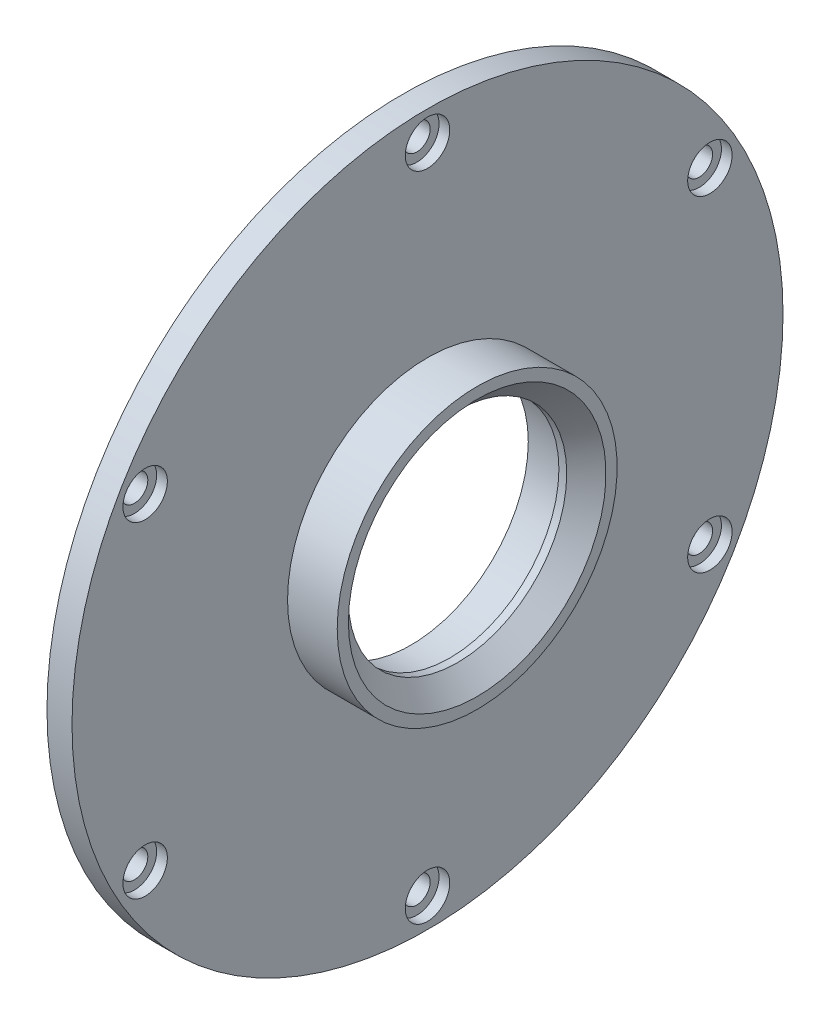
SolidWorks part; units mm, degrees
ref_plane "Front Plane" through (0, 0, 0) normal (0, 0, 1) x (1, 0, 0)
ref_plane "Top Plane" through (0, 0, 0) normal (0, 1, 0) x (1, 0, 0)
ref_plane "Right Plane" through (0, 0, 0) normal (1, 0, 0) x (0, 0, -1)
sketch "Sketch2" plane through (0, 0, 0) normal (0, 0, 1) x (1, 0, 0)
  line L0 (0, 0) -> (58.591, 0) construction
  line L2 (0, 0) -> (18.4, 0)
  line L3 (0, 0) -> (0, 2.5)
  line L4 (0, 2.5) -> (18.4, 2.5)
  line L5 (18.4, 0) -> (18.4, 2.5)
  line L6 (6.0094, 2.5) -> (6.0094, 6)
  line L11 (6.0094, 6) -> (9.9794, 6)
  line L16 (12.9794, 6) -> (12.9794, 3)
  line L17 (12.9794, 3) -> (13.6398, 3)
  line L18 (13.6398, 3) -> (13.6398, 2.5)
  line L19 (13.6398, 2.5) -> (6.0094, 2.5)
  line L22 (13.6398, 2.5) -> (16.1198, 2.5)
  line L23 (13.6398, 2.5) -> (13.6398, 4)
  line L24 (13.6398, 4) -> (16.1198, 4)
  line L25 (16.1198, 2.5) -> (16.1198, 4)
  line L27 (6.0094, 6) -> (9.9794, 6)
  line L28 (6.0094, 6) -> (6.0094, 9)
  line L29 (6.0094, 9) -> (9.9794, 9)
  line L30 (9.9794, 6) -> (9.9794, 9)
  line L31 (6.0094, 9) -> (6.0094, 8.25)
  line L32 (6.0094, 8.25) -> (5.0094, 8.25)
  line L33 (8.6609, 22.001) -> (8.6609, 12.476) construction
  line L34 (5.0094, 12.476) -> (12.3124, 12.476)
  line L35 (9.9794, 9) -> (12.3124, 9)
  line L36 (5.0094, 7.9375) -> (1.7709, 7.9375)
  line L37 (5.0094, 8.25) -> (5.0094, 12.476)
  line L38 (5.0094, 7.9375) -> (5.0094, 13.9365)
  line L39 (5.0094, 13.9365) -> (1.7709, 13.9365)
  line L40 (1.7709, 7.9375) -> (1.7709, 13.9365)
  line L41 (5.0094, 22.001) -> (12.3124, 22.001)
  line L42 (5.0094, 22.001) -> (5.0094, 30.1625)
  line L43 (5.0094, 30.1625) -> (12.3124, 30.1625)
  line L44 (12.3124, 22.001) -> (12.3124, 30.1625)
  line L49 (16.6398, 22.001) -> (16.6398, 7.5)
  line L51 (23.0198, 7.5) -> (23.0198, 6.5)
  line L54 (16.1198, 4) -> (13.6398, 4)
  line L56 (18.0398, 7.5) -> (23.0198, 7.5)
  line L57 (13.3124, 22.001) -> (16.6398, 22.001)
  line L58 (16.1198, 3.5) -> (20.0198, 3.5)
  line L59 (29.9098, 14) -> (26.9098, 11)
  line L60 (4.0094, 31.75) -> (18.0398, 31.75)
  line L61 (18.0398, 7.5) -> (23.0198, 7.5)
  line L62 (18.0398, 7.5) -> (18.0398, 12)
  line L63 (18.0398, 12) -> (23.0198, 12)
  line L64 (23.0198, 7.5) -> (23.0198, 12)
  line L65 (18.0398, 31.75) -> (18.0398, 12)
  line L66 (23.0198, 11) -> (26.9098, 11)
  line L67 (34.8098, 23) -> (31.3098, 19.5)
  line L68 (35.8098, 31) -> (38.7998, 33.99)
  line L69 (29.9098, 14) -> (29.9098, 15)
  line L70 (29.9098, 15) -> (22.9398, 15)
  line L71 (22.9398, 15) -> (21.0398, 15)
  line L72 (18.0398, 7.5) -> (16.6398, 7.5)
  line L73 (21.0398, 15) -> (21.0398, 43)
  line L74 (19.6115, 40) -> (9.6516, 40)
  line L75 (9.6516, 40) -> (4.0094, 40)
  line L76 (21.0398, 43) -> (19.6115, 43)
  line L77 (22.9398, 15) -> (29.9098, 15)
  line L78 (22.9398, 15) -> (22.9398, 21)
  line L79 (22.9398, 21) -> (29.9098, 21)
  line L80 (29.9098, 15) -> (29.9098, 21)
  line L81 (9.6516, 40) -> (19.6115, 40)
  line L82 (9.6516, 40) -> (9.6516, 50)
  line L83 (9.6516, 50) -> (19.6115, 50)
  line L84 (19.6115, 40) -> (19.6115, 50)
  line L85 (4.0094, 40) -> (4.0094, 31.75)
  line L86 (12.9794, 3) -> (12.9794, 2.5)
  line L87 (31.3098, 19.5) -> (29.9098, 19.5)
  line L88 (21.4694, 63.5) -> (21.4694, 51.308)
  line L89 (21.4694, 63.5) -> (25.9398, 63.5)
  line L90 (25.9398, 63.5) -> (25.9398, 25)
  line L91 (27.8398, 25) -> (25.9398, 25)
  line L92 (9.6516, 48) -> (8.2233, 48)
  line L93 (8.2233, 48) -> (8.2233, 53.476)
  line L94 (8.2233, 53.476) -> (19.6115, 53.476)
  line L95 (19.6115, 53.476) -> (19.6115, 50)
  line L96 (13.9174, 63.001) -> (13.9174, 53.476) construction
  line L97 (8.2233, 63.001) -> (19.6115, 63.001)
  line L98 (8.2233, 63.001) -> (8.2233, 68.2625)
  line L99 (8.2233, 68.2625) -> (19.6115, 68.2625)
  line L100 (19.6115, 63.001) -> (19.6115, 68.2625)
  line L101 (12.9794, 6) -> (11.9794, 6)
  line L102 (8.2233, 44.825) -> (4.9848, 44.825)
  line L103 (8.2233, 44.825) -> (8.2233, 54.9365)
  line L104 (8.2233, 54.9365) -> (4.9848, 54.9365)
  line L106 (9.9794, 6) -> (10.8794, 6)
  line L107 (27.8398, 25) -> (34.8098, 25)
  line L108 (34.8098, 25) -> (34.8098, 23)
  line L109 (0, 0) -> (-2, 0)
  line L110 (0, 0) -> (0, 11)
  line L111 (27.8398, 25) -> (34.8098, 25)
  line L112 (27.8398, 25) -> (27.8398, 32.5)
  line L113 (27.8398, 32.5) -> (34.8098, 32.5)
  line L114 (34.8098, 25) -> (34.8098, 32.5)
  line L115 (35.8098, 31) -> (34.8098, 31)
  line L116 (27.8398, 32.5) -> (27.8398, 64.5)
  line L117 (20.5849, 74.025) -> (6.2499, 74.025)
  line L118 (6.2499, 74.025) -> (6.2499, 76.2)
  line L119 (38.7998, 47.29) -> (30.8398, 55.25)
  line L120 (0, 11) -> (-2, 11)
  line L121 (38.7998, 43.815) -> (30.8623, 43.815)
  line L123 (-4.8152, 69.85) -> (1.5348, 76.2)
  line L124 (38.7998, 47.29) -> (38.7998, 33.99)
  line L125 (-2, 0) -> (-2, 11)
  line L126 (38.7998, 37.465) -> (30.8623, 37.465)
  line L127 (30.8623, 43.815) -> (30.8623, 37.465)
  line L128 (6.0094, 2.5) -> (6.0094, 0)
  line L129 (-0.0152, 63.5) -> (-0.0152, 30)
  line L132 (4.9848, 63.5) -> (-0.0152, 63.5)
  line L136 (-1.8152, 30) -> (-11.7752, 30)
  line L138 (-13.7752, 25.4) -> (-2, 25.4)
  line L139 (-2, 25.4) -> (-2, 11.5)
  line L140 (27.8398, 64.5) -> (20.5849, 64.5)
  line L141 (-1.8152, 30) -> (-11.7752, 30)
  line L142 (-1.8152, 30) -> (-1.8152, 39)
  line L143 (-1.8152, 39) -> (-11.7752, 39)
  line L144 (-11.7752, 30) -> (-11.7752, 39)
  line L145 (20.5849, 64.5) -> (20.5849, 74.025)
  line L146 (-12.7752, 37) -> (-12.7752, 47.29)
  line L147 (-12.7752, 37) -> (-11.7752, 37)
  line L148 (30.8398, 55.25) -> (30.8398, 76.2)
  line L149 (11.9794, 6) -> (11.9794, 5.45)
  line L154 (-2, 11.5) -> (0.5, 11.5)
  line L155 (4.9848, 60.6197) -> (24.0348, 60.6197)
  line L160 (4.9848, 60.6197) -> (4.9848, 55.8572)
  line L161 (4.9848, 55.8572) -> (24.0348, 55.8572)
  line L166 (24.0348, 60.6197) -> (24.0348, 55.8572)
  line L167 (4.9848, 60.6197) -> (24.0348, 55.8572) construction
  line L172 (4.9848, 55.8572) -> (24.0348, 60.6197) construction
  line L173 (24.0348, 62.2072) -> (25.9398, 62.2072)
  line L174 (11.9794, 5.45) -> (10.8794, 5.45)
  line L175 (10.8794, 6) -> (10.8794, 5.45)
  line L176 (24.0348, 62.2072) -> (24.0348, 54.2697)
  line L177 (24.0348, 54.2697) -> (25.9398, 54.2697)
  line L178 (25.9398, 62.2072) -> (25.9398, 54.2697)
  line L179 (24.0348, 62.2072) -> (25.9398, 54.2697) construction
  line L180 (24.0348, 54.2697) -> (25.9398, 62.2072) construction
  line L181 (3, 19.6197) -> (15.7, 19.6197)
  line L182 (3, 19.6197) -> (3, 14.8572)
  line L183 (3, 14.8572) -> (15.7, 14.8572)
  line L184 (15.7, 19.6197) -> (15.7, 14.8572)
  line L185 (3, 19.6197) -> (15.7, 14.8572) construction
  line L186 (3, 14.8572) -> (15.7, 19.6197) construction
  line L187 (15.7, 21.2072) -> (16.6398, 21.2072)
  line L188 (15.7, 21.2072) -> (15.7, 13.2697)
  line L189 (15.7, 13.2697) -> (16.6398, 13.2697)
  line L190 (16.6398, 21.2072) -> (16.6398, 13.2697)
  line L191 (15.7, 21.2072) -> (16.6398, 13.2697) construction
  line L192 (15.7, 13.2697) -> (16.6398, 21.2072) construction
  line L193 (0.5, 11.5) -> (0.5, 6.9375)
  line L194 (0.5, 6.9375) -> (1.7709, 6.9375)
  line L195 (23.0198, 6.5) -> (20.0198, 3.5)
  line L196 (4.9848, 63.5) -> (4.9848, 54.9365)
  line L197 (3, 43.825) -> (4.9848, 43.825)
  line L198 (1.7709, 6.9375) -> (1.7709, 7.9375)
  line L199 (6.0094, 0) -> (12.9794, 0)
  line L200 (12.9794, 0) -> (12.9794, 2.5)
  line L201 (18.0398, 31.75) -> (18.0398, 35.875)
  line L202 (18.0398, 35.875) -> (21.0398, 35.875)
  line L203 (30.8398, 76.2) -> (6.2499, 76.2)
  line L204 (2.8049, 69.85) -> (7.2499, 69.85) construction
  line L205 (7.2499, 67.4688) -> (26.2999, 67.4688)
  line L206 (7.2499, 74.025) -> (7.2499, 64.5)
  line L207 (7.2499, 64.5) -> (-1.8152, 64.5)
  line L208 (-1.8152, 64.5) -> (-1.8152, 39)
  line L209 (-12.7752, 47.29) -> (-4.8152, 55.25)
  line L210 (-4.8152, 55.25) -> (-4.8152, 69.85)
  line L211 (7.2499, 67.4688) -> (7.2499, 72.2312)
  line L212 (7.2499, 72.2312) -> (26.2999, 72.2313)
  line L213 (26.2999, 67.4688) -> (26.2999, 72.2313)
  line L214 (26.2999, 73.8187) -> (30.8398, 73.8187)
  line L215 (26.2999, 73.8187) -> (26.2999, 65.8813)
  line L216 (26.2999, 65.8813) -> (30.8398, 65.8813)
  line L217 (30.8398, 73.8187) -> (30.8398, 65.8813)
  line L218 (2.8049, 72.2313) -> (25.0299, 72.2313)
  line L219 (2.8049, 72.2313) -> (2.8049, 67.4687)
  line L220 (2.8049, 67.4687) -> (25.0299, 67.4687)
  line L221 (25.0299, 72.2313) -> (25.0299, 67.4687)
  line L222 (25.0299, 69.85) -> (20.5849, 69.85) construction
  line L223 (21.4694, 51.308) -> (22.9398, 51.308)
  line L224 (22.9398, 51.308) -> (22.9398, 21)
  line L225 (13.6398, 4) -> (13.6398, 12.2697)
  line L226 (13.6398, 12.2697) -> (13.3124, 12.2697)
  line L227 (13.3124, 12.2697) -> (13.3124, 22.001)
  line L228 (12.3124, 9) -> (12.3124, 12.476)
  line L229 (-1.8152, 30) -> (-0.0152, 30)
  line L230 (8.2233, 65.6317) -> (2.8049, 65.6317) construction
  line L231 (19.6115, 65.6317) -> (25.0299, 65.6317) construction
  line L232 (1.5348, 76.2) -> (6.2499, 76.2)
  line L233 (-11.7752, 30) -> (-13.7752, 30)
  line L234 (-13.7752, 30) -> (-13.7752, 25.4)
  line L235 (3, 13.9365) -> (3, 43.825)
  line L236 (4.9848, 54.9365) -> (4.9848, 44.825)
  line L237 (4.9848, 43.825) -> (4.9848, 44.825)
  circle A0 centre (26.8898, 25.95) radius 0.95
  circle A1 centre (21.9898, 15.95) radius 0.95
  circle A2 centre (17.3398, 8.2) radius 0.7
  circle A3 centre (10.4294, 6.45) radius 0.45
  circle A4 centre (-0.9152, 30.9) radius 0.9
  point P7 (24.9873, 58.2385)
  point P131 (16.1699, 17.2385)
  point P135 (14.5098, 58.2385)
  point P146 (9.35, 17.2385)
sketch "Sketch3" plane through (0, 0, 0) normal (0, 0, 1) x (1, 0, 0)
  line L0 (34.8098, 25) -> (34.8098, 23) construction
  line L4 (29.9098, 15) -> (29.9098, 21) construction
  line L5 (31.3098, 19.5) -> (29.9098, 19.5) construction
  line L6 (34.8098, 23) -> (31.3098, 19.5) construction
  line L7 (22.9398, 21) -> (29.9098, 21) construction
  line L11 (34.8098, 25) -> (34.8098, 23)
  line L15 (29.9098, 19.5) -> (29.9098, 21)
  line L16 (31.3098, 19.5) -> (29.9098, 19.5)
  line L17 (34.8098, 23) -> (31.3098, 19.5)
  line L18 (22.9398, 21) -> (29.9098, 21)
  line L22 (27.8398, 25) -> (25.9398, 25) construction
  line L23 (27.8398, 25) -> (34.8098, 25) construction
  line L24 (25.9398, 63.5) -> (25.9398, 25) construction
  line L25 (22.9398, 51.308) -> (22.9398, 21) construction
  line L26 (21.4694, 51.308) -> (22.9398, 51.308) construction
  line L27 (21.4694, 63.5) -> (21.4694, 51.308) construction
  line L28 (21.4694, 63.5) -> (25.9398, 63.5) construction
  line L29 (27.8398, 25) -> (25.9398, 25)
  line L30 (27.8398, 25) -> (34.8098, 25)
  line L31 (25.9398, 63.5) -> (25.9398, 25)
  line L32 (22.9398, 51.308) -> (22.9398, 21)
  line L33 (21.4694, 51.308) -> (22.9398, 51.308)
  line L34 (21.4694, 63.5) -> (21.4694, 51.308)
  line L35 (21.4694, 63.5) -> (25.9398, 63.5)
revolve "Revolve1" add sketch "Sketch3" angle 360 about L0
sketch "Sketch4" plane through (0, 0, 0) normal (1, 0, 0) x (0, 0, -1)
  line L0 (0, 0) -> (0, 69.85) construction
  line L1 (0, 0) -> (13.6271, 68.5079) construction
  line L2 (0, 0) -> (0, 58.2385) construction
  line L3 (0, 0) -> (50.436, 29.1192) construction
  line L4 (0, 0) -> (0, 31.75) construction
  line L5 (0, 0) -> (12.1502, 29.3332) construction
  line L6 (0, 0) -> (0, 17.2385) construction
  line L7 (0, 0) -> (14.929, 8.6192) construction
  line L8 (0, 0) -> (0, 58.2385) construction
  line L9 (0, 0) -> (50.436, 29.1192) construction
  line L10 (0, 0) -> (5.9583, 29.9542) construction
  line L11 (0, 0) -> (16.9677, 25.394) construction
  circle A0 centre (0, 0) radius 69.85 construction
  circle A1 centre (0, 0) radius 58.2385 construction
  circle A2 centre (0, 0) radius 31.75 construction
  circle A3 centre (0, 0) radius 17.2385 construction
  circle A4 centre (0, 69.85) radius 3.175
  circle A5 centre (0, 58.2385) radius 4.7625
  circle A6 centre (0, 31.75) radius 3.175
  circle A7 centre (0, 17.2385) radius 4.7625
  circle A8 centre (13.6271, 68.5079) radius 3.175
  circle A9 centre (26.7304, 64.533) radius 3.175
  circle A10 centre (38.8066, 58.0782) radius 3.175
  circle A11 centre (49.3914, 49.3914) radius 3.175
  circle A12 centre (58.0782, 38.8066) radius 3.175
  circle A13 centre (64.533, 26.7304) radius 3.175
  circle A14 centre (68.5079, 13.6271) radius 3.175
  circle A15 centre (69.85, 0) radius 3.175
  circle A16 centre (68.5079, -13.6271) radius 3.175
  circle A17 centre (64.533, -26.7304) radius 3.175
  circle A18 centre (58.0782, -38.8066) radius 3.175
  circle A19 centre (49.3914, -49.3914) radius 3.175
  circle A20 centre (38.8066, -58.0782) radius 3.175
  circle A21 centre (26.7304, -64.533) radius 3.175
  circle A22 centre (13.6271, -68.5079) radius 3.175
  circle A23 centre (0, -69.85) radius 3.175
  circle A24 centre (-13.6271, -68.5079) radius 3.175
  circle A25 centre (-26.7304, -64.533) radius 3.175
  circle A26 centre (-38.8066, -58.0782) radius 3.175
  circle A27 centre (-49.3914, -49.3914) radius 3.175
  circle A28 centre (-58.0782, -38.8066) radius 3.175
  circle A29 centre (-64.533, -26.7304) radius 3.175
  circle A30 centre (-68.5079, -13.6271) radius 3.175
  circle A31 centre (-69.85, 0) radius 3.175
  circle A32 centre (-68.5079, 13.6271) radius 3.175
  circle A33 centre (-64.533, 26.7304) radius 3.175
  circle A34 centre (-58.0782, 38.8066) radius 3.175
  circle A35 centre (-49.3914, 49.3914) radius 3.175
  circle A36 centre (-38.8066, 58.0782) radius 3.175
  circle A37 centre (-26.7304, 64.533) radius 3.175
  circle A38 centre (-13.6271, 68.5079) radius 3.175
  circle A47 centre (50.436, 29.1192) radius 4.7625
  circle A48 centre (50.436, -29.1192) radius 4.7625
  circle A49 centre (0, -58.2385) radius 4.7625
  circle A50 centre (-50.436, -29.1192) radius 4.7625
  circle A51 centre (-50.436, 29.1192) radius 4.7625
  circle A58 centre (12.1502, 29.3332) radius 3.175
  circle A59 centre (22.4506, 22.4506) radius 3.175
  circle A60 centre (29.3332, 12.1502) radius 3.175
  circle A61 centre (31.75, 0) radius 3.175
  circle A62 centre (29.3332, -12.1502) radius 3.175
  circle A63 centre (22.4506, -22.4506) radius 3.175
  circle A64 centre (12.1502, -29.3332) radius 3.175
  circle A65 centre (0, -31.75) radius 3.175
  circle A66 centre (-12.1502, -29.3332) radius 3.175
  circle A67 centre (-22.4506, -22.4506) radius 3.175
  circle A68 centre (-29.3332, -12.1502) radius 3.175
  circle A69 centre (-31.75, 0) radius 3.175
  circle A70 centre (-29.3332, 12.1502) radius 3.175
  circle A71 centre (-22.4506, 22.4506) radius 3.175
  circle A72 centre (14.929, 8.6192) radius 4.7625
  circle A73 centre (14.929, -8.6192) radius 4.7625
  circle A74 centre (0, -17.2385) radius 4.7625
  circle A75 centre (-14.929, -8.6192) radius 4.7625
  circle A76 centre (-14.929, 8.6192) radius 4.7625
  circle A77 centre (0, 0) radius 50
  circle A78 centre (0, 0) radius 9
  circle A79 centre (-12.1502, 29.3332) radius 3.175
  circle A80 centre (0, 0) radius 76.2
  circle A81 centre (0, 0) radius 74.025
  circle A82 centre (0, 69.85) radius 3.9687
  circle A83 centre (49.3914, 49.3914) radius 3.9687
  circle A84 centre (69.85, 0) radius 3.9688
  circle A85 centre (49.3914, -49.3914) radius 3.9687
  circle A86 centre (0, -69.85) radius 3.9687
  circle A87 centre (-49.3914, -49.3914) radius 3.9687
  circle A88 centre (-69.85, 0) radius 3.9688
  circle A89 centre (-49.3914, 49.3914) radius 3.9687
  circle A90 centre (0, 69.85) radius 2.3812
  circle A91 centre (13.6271, 68.5079) radius 2.3812
  circle A92 centre (26.7304, 64.533) radius 2.3813
  circle A93 centre (38.8066, 58.0782) radius 2.3812
  circle A94 centre (49.3914, 49.3914) radius 2.3812
  circle A95 centre (58.0782, 38.8066) radius 2.3812
  circle A96 centre (64.533, 26.7304) radius 2.3813
  circle A97 centre (68.5079, 13.6271) radius 2.3813
  circle A98 centre (69.85, 0) radius 2.3813
  circle A99 centre (68.5079, -13.6271) radius 2.3813
  circle A100 centre (64.533, -26.7304) radius 2.3813
  circle A101 centre (58.0782, -38.8066) radius 2.3812
  circle A102 centre (49.3914, -49.3914) radius 2.3812
  circle A103 centre (38.8066, -58.0782) radius 2.3812
  circle A104 centre (26.7304, -64.533) radius 2.3813
  circle A105 centre (13.6271, -68.5079) radius 2.3812
  circle A106 centre (0, -69.85) radius 2.3812
  circle A107 centre (-13.6271, -68.5079) radius 2.3812
  circle A108 centre (-26.7304, -64.533) radius 2.3813
  circle A109 centre (-38.8066, -58.0782) radius 2.3812
  circle A110 centre (-49.3914, -49.3914) radius 2.3812
  circle A111 centre (-58.0782, -38.8066) radius 2.3812
  circle A112 centre (-64.533, -26.7304) radius 2.3812
  arc A113 (3.0399, 30.8338) -> (8.9911, 29.65) centre (5.9583, 29.9542) cw
  arc A114 (14.6081, 27.3234) -> (19.6532, 23.9523) centre (16.9677, 25.394) cw
  arc A115 (23.9523, 19.6532) -> (27.3234, 14.6081) centre (25.394, 16.9677) cw
  arc A116 (29.65, 8.9911) -> (30.8338, 3.0399) centre (29.9542, 5.9583) cw
  arc A117 (30.8338, -3.0399) -> (29.65, -8.9911) centre (29.9542, -5.9583) cw
  arc A118 (27.3234, -14.6081) -> (23.9523, -19.6532) centre (25.394, -16.9677) cw
  arc A119 (19.6532, -23.9523) -> (14.6081, -27.3234) centre (16.9677, -25.394) cw
  arc A120 (8.9911, -29.65) -> (3.0399, -30.8338) centre (5.9583, -29.9542) cw
  arc A121 (-3.0399, -30.8338) -> (-8.9911, -29.65) centre (-5.9583, -29.9542) cw
  arc A122 (-14.6081, -27.3234) -> (-19.6532, -23.9523) centre (-16.9677, -25.394) cw
  arc A123 (-23.9523, -19.6532) -> (-27.3234, -14.6081) centre (-25.394, -16.9677) cw
  arc A124 (-29.65, -8.9911) -> (-30.8338, -3.0399) centre (-29.9542, -5.9583) cw
  arc A125 (-30.8338, 3.0399) -> (-29.65, 8.9911) centre (-29.9542, 5.9583) cw
  arc A126 (-27.3234, 14.6081) -> (-23.9523, 19.6532) centre (-25.394, 16.9677) cw
  arc A127 (-19.6532, 23.9523) -> (-14.6081, 27.3234) centre (-16.9677, 25.394) cw
  arc A128 (-8.9911, 29.65) -> (-3.0399, 30.8338) centre (-5.9583, 29.9542) cw
  arc A129 (26.9875, 0) -> (26.9932, 0.1932) centre (30.2705, 0) cw
  arc A130 (65.0988, 0.2771) -> (65.0875, 0) centre (68.4964, 0) ccw
  circle A131 centre (1.5875, 0) radius 40
  circle A132 centre (1.5875, 0) radius 2.5
  circle A133 centre (1.5875, 0) radius 3
  circle A134 centre (1.5875, 0) radius 43
  circle A135 centre (-68.5079, -13.6271) radius 2.3813
  circle A136 centre (-69.85, 0) radius 2.3813
  circle A137 centre (-68.5079, 13.6271) radius 2.3813
  circle A138 centre (-64.533, 26.7304) radius 2.3812
  circle A139 centre (-58.0782, 38.8066) radius 2.3812
  circle A140 centre (-49.3914, 49.3914) radius 2.3812
  circle A141 centre (-38.8066, 58.0782) radius 2.3812
  circle A142 centre (-26.7304, 64.533) radius 2.3813
  circle A143 centre (-13.6271, 68.5079) radius 2.3812
  circle A144 centre (0, 58.2385) radius 2.3812
  circle A145 centre (0, 58.2385) radius 3.9688
  circle A146 centre (50.436, 29.1192) radius 3.9688
  circle A147 centre (50.436, 29.1192) radius 2.3813
  circle A148 centre (50.436, -29.1192) radius 3.9687
  circle A149 centre (50.436, -29.1192) radius 2.3812
  circle A150 centre (0, -58.2385) radius 3.9687
  circle A151 centre (0, -58.2385) radius 2.3812
  circle A152 centre (-50.436, -29.1192) radius 3.9687
  circle A153 centre (-50.436, -29.1192) radius 2.3812
  circle A154 centre (-50.436, 29.1192) radius 3.9687
  circle A155 centre (-50.436, 29.1192) radius 2.3812
  spline S1 degree 4 poles (26.9875, 0) (26.9875, -0.0248) (26.9882, -0.0743) (26.9912, -0.1613) (26.9992, -0.2849) (27.0142, -0.4323) (27.0403, -0.5994) (27.0821, -0.7965) (27.1455, -1.0177) (27.2241, -1.2336) (27.3173, -1.4437) (27.4329, -1.6623) (27.5739, -1.8864) (27.7427, -2.1125) (27.9417, -2.3365) (28.1305, -2.5184) (28.3007, -2.6647) (28.4457, -2.7828) (28.5617, -2.8775) (28.6745, -2.9758) (28.7813, -3.0807) (28.9057, -3.2206) (29.0482, -3.4108) (29.197, -3.6576) (29.3758, -4.0447) (29.5291, -4.5502) (29.6152, -5.1612) (29.5933, -5.8758) (29.4507, -6.5869) (29.186, -7.2733) (28.8461, -7.831) (28.4818, -8.2549) (28.1375, -8.5536) (27.8792, -8.7284) (27.6484, -8.8496) (27.4154, -8.9438) (27.2144, -9.0029) (27.0118, -9.0554) (26.7709, -9.1263) (26.5334, -9.2082) (26.2634, -9.3231) (25.9685, -9.4827) (25.5538, -9.7623) (25.0678, -10.2216) (24.6281, -10.8948) (24.3613, -11.7878) (24.3459, -12.6097) (24.4764, -13.2366) (24.6525, -13.7006) (24.8058, -14.0202) (24.9382, -14.271) (25.0503, -14.5321) (25.1258, -14.8064) (25.1736, -15.0995) (25.1911, -15.4094) (25.1742, -15.8163) (25.0891, -16.3148) (24.907, -16.8764) (24.5182, -17.6315) (23.9757, -18.2942) (23.3695, -18.7764) (22.7564, -19.084) (22.3641, -19.2199) (22.0554, -19.2923) (21.7533, -19.3289) (21.4612, -19.3296) (21.1723, -19.2896) (20.8852, -19.2417) (20.5956, -19.2104) (20.3043, -19.1994) (19.8669, -19.2177) (19.2899, -19.3231) (18.5833, -19.6092) (17.8444, -20.1834) (17.3807, -20.828) (17.1316, -21.424) (17.0182, -21.8879) (16.9714, -22.1971) (16.9537, -22.4701) (16.9533, -22.7044) (16.9619, -22.9384) (16.9737, -23.1333) (16.977, -23.3286) (16.9594, -23.5624) (16.9177, -23.8101) (16.834, -24.1055) (16.6578, -24.5276) (16.3623, -25.0151) (15.9278, -25.5198) (15.3432, -25.99) (14.6957, -26.3472) (14.0068, -26.5857) (13.3856, -26.6851) (12.847, -26.6849) (12.4166, -26.6224) (12.1324, -26.5468) (11.9058, -26.4598) (11.7342, -26.3753) (11.6017, -26.2989) (11.4727, -26.2169) (11.3444, -26.1337) (11.1825, -26.0322) (10.9836, -25.9179) (10.7435, -25.7991) (10.4587, -25.6867) (10.0106, -25.5536) (9.3843, -25.468) (8.599, -25.5363) (7.7243, -25.8773) (7.1093, -26.3459) (6.716, -26.8042) (6.4745, -27.1841) (6.3352, -27.4489) (6.215, -27.7227) (6.1113, -28.0028) (5.9959, -28.2789) (5.841, -28.5357) (5.6522, -28.7792) (5.4316, -29.007) (5.1188, -29.2711) (4.6965, -29.5439) (4.1624, -29.7882) (3.5487, -29.9564) (2.9521, -30.0296) (2.386, -30.0225) (1.8595, -29.949) (1.3409, -29.8055) (0.9058, -29.6147) (0.5544, -29.4004) (0.2828, -29.1832) (0.0847, -28.9875) (-0.0865, -28.768) (-0.2353, -28.5332) (-0.3904, -28.3016) (-0.5598, -28.0786) (-0.792, -27.8146) (-1.1036, -27.5274) (-1.5105, -27.2448) (-2.0688, -26.9834) (-2.7167, -26.8202) (-3.459, -26.7949) (-4.1529, -26.9407) (-4.7224, -27.1899) (-5.1296, -27.455) (-5.3866, -27.661) (-5.5925, -27.8507) (-5.7558, -28.014) (-5.9199, -28.1766) (-6.0977, -28.3246) (-6.3382, -28.4851) (-6.6906, -28.6628) (-7.1669, -28.8182) (-7.7668, -28.9076) (-8.4201, -28.8957) (-9.0747, -28.7804) (-9.7144, -28.5614) (-10.3217, -28.2381) (-10.8061, -27.8636) (-11.1671, -27.4837) (-11.4143, -27.1402) (-11.5734, -26.859) (-11.6946, -26.573) (-11.7735, -26.2857) (-11.8173, -25.9915) (-11.8668, -25.6988) (-11.9353, -25.4093) (-12.0257, -25.1261) (-12.198, -24.7091) (-12.5089, -24.187) (-13.0379, -23.6191) (-13.8448, -23.1355) (-14.6072, -22.9365) (-15.2369, -22.9149) (-15.701, -22.9694) (-16.0024, -23.0316) (-16.2609, -23.107) (-16.4782, -23.1841) (-16.6576, -23.2529) (-16.8015, -23.307) (-16.9839, -23.3672) (-17.2087, -23.4203) (-17.4853, -23.4534) (-17.811, -23.4543) (-18.2291, -23.4104) (-18.7305, -23.2885) (-19.2884, -23.06) (-19.8603, -22.7052) (-20.3581, -22.2764) (-20.7758, -21.7899) (-21.1086, -21.2598) (-21.3336, -20.7318) (-21.4619, -20.2263) (-21.5006, -19.8113) (-21.4889, -19.4989) (-21.4468, -19.2424) (-21.3965, -19.0408) (-21.34, -18.8332) (-21.2878, -18.6168) (-21.2341, -18.3322) (-21.1962, -17.9773) (-21.1985, -17.5604) (-21.2781, -17.0173) (-21.4721, -16.4256) (-21.838, -15.7861) (-22.3482, -15.2578) (-22.8946, -14.8957) (-23.3828, -14.6878) (-23.7368, -14.5834) (-24.0536, -14.5215) (-24.3285, -14.4876) (-24.6045, -14.47) (-24.8811, -14.458) (-25.1556, -14.4184) (-25.4228, -14.3439) (-25.6932, -14.2375) (-26.1109, -14.0218) (-26.5677, -13.6822) (-27.0258, -13.1981) (-27.4314, -12.5682) (-27.7017, -11.9578) (-27.8746, -11.3112) (-27.9332, -10.727) (-27.9111, -10.2247) (-27.8415, -9.8214) (-27.7568, -9.5159) (-27.6427, -9.2298) (-27.5004, -8.9659) (-27.3212, -8.7261) (-27.1301, -8.4966) (-26.9071, -8.1967) (-26.6417, -7.7583) (-26.3997, -7.1508) (-26.2841, -6.3875) (-26.3642, -5.5798) (-26.6019, -4.9055) (-26.9193, -4.3761) (-27.2736, -3.9636) (-27.583, -3.6904) (-27.8719, -3.4871) (-28.1186, -3.3407) (-28.3135, -3.2371) (-28.5043, -3.1411) (-28.6854, -3.0419) (-28.9002, -2.8984) (-29.1355, -2.6958) (-29.4123, -2.3882) (-29.6958, -1.9552) (-29.932, -1.437) (-30.0985, -0.839) (-30.1779, -0.2025) (-30.1603, 0.4599) (-30.0348, 1.1323) (-29.8199, 1.711) (-29.5617, 2.1719) (-29.3035, 2.5118) (-29.0784, 2.748) (-28.8655, 2.924) (-28.6761, 3.0468) (-28.5112, 3.1367) (-28.3775, 3.205) (-28.2106, 3.2911) (-28.0136, 3.4005) (-27.7912, 3.5413) (-27.5508, 3.7219) (-27.2011, 4.0343) (-26.7941, 4.5285) (-26.4419, 5.234) (-26.2777, 6.1494) (-26.351, 6.9081) (-26.5268, 7.4739) (-26.7218, 7.8823) (-26.8619, 8.1196) (-26.9953, 8.3144) (-27.1373, 8.5028) (-27.2613, 8.6553) (-27.3845, 8.8088) (-27.518, 9.0035) (-27.6324, 9.2103) (-27.7412, 9.4693) (-27.8326, 9.7814) (-27.9074, 10.1885) (-27.9345, 10.6913) (-27.8808, 11.2771) (-27.6878, 12.0229) (-27.3166, 12.8111) (-26.8405, 13.4278) (-26.3243, 13.8718) (-25.9118, 14.1263) (-25.6503, 14.2566) (-25.3769, 14.3596) (-25.0933, 14.4318) (-24.8027, 14.4634) (-24.5112, 14.4738) (-24.1629, 14.5033) (-23.7608, 14.5717) (-23.1887, 14.7443) (-22.5511, 15.0901) (-21.962, 15.6231) (-21.544, 16.2749) (-21.3217, 16.857) (-21.2175, 17.3851) (-21.1902, 17.8397) (-21.2185, 18.2374) (-21.2771, 18.5739) (-21.3443, 18.8506) (-21.405, 19.0706) (-21.4579, 19.2928) (-21.4883, 19.5194) (-21.4981, 19.805) (-21.4664, 20.1907) (-21.3565, 20.6672) (-21.1331, 21.2135) (-20.8025, 21.7541) (-20.3882, 22.2461) (-19.8974, 22.677) (-19.3379, 23.033) (-18.7964, 23.2649) (-18.309, 23.3941) (-17.8981, 23.4483) (-17.5726, 23.4572) (-17.2924, 23.4331) (-17.0602, 23.3874) (-16.8337, 23.3199) (-16.6495, 23.2499) (-16.4659, 23.1791) (-16.2424, 23.1025) (-16.0156, 23.0362) (-15.7461, 22.9768) (-15.2967, 22.9185) (-14.7035, 22.9278) (-13.9592, 23.0948) (-13.1407, 23.5365) (-12.5805, 24.0908) (-12.2382, 24.6309) (-12.0505, 25.0599) (-11.9538, 25.3442) (-11.8892, 25.5989) (-11.8463, 25.8198) (-11.8162, 26.0048) (-11.7926, 26.153) (-11.7577, 26.3372) (-11.6989, 26.5548) (-11.5969, 26.8111) (-11.4414, 27.0975) (-11.1977, 27.4473) (-10.8392, 27.8343) (-10.3554, 28.2166) (-9.7549, 28.5431) (-9.1303, 28.7642) (-8.5, 28.8851) (-7.879, 28.911) (-7.3126, 28.8458) (-6.8128, 28.7091) (-6.4345, 28.54) (-6.1692, 28.378) (-5.9665, 28.2173) (-5.8163, 28.0752) (-5.6659, 27.9232) (-5.5067, 27.7699) (-5.2907, 27.5806) (-5.0072, 27.369) (-4.6509, 27.1597) (-4.148, 26.9513) (-3.5452, 26.8146) (-2.8302, 26.7991) (-2.0381, 26.9749) (-1.3495, 27.3225) (-0.8483, 27.741) (-0.5146, 28.1291) (-0.2991, 28.4338) (-0.1401, 28.6862) (0.0331, 28.93) (0.2405, 29.146) (0.4774, 29.3422) (0.7418, 29.5165) (1.1036, 29.7066) (1.5741, 29.882) (2.1471, 30.006) (2.8151, 30.041) (3.4791, 29.9721) (4.2039, 29.7804) (4.8064, 29.4933) (5.2708, 29.1628) (5.6049, 28.8311) (5.7894, 28.6062) (5.9424, 28.3744) (6.0642, 28.1249) (6.161, 27.8653) (6.2635, 27.608) (6.3813, 27.357) (6.5388, 27.0748) (6.7484, 26.7704) (7.0986, 26.3707) (7.6135, 25.9641) (8.2747, 25.644) (8.9962, 25.4959) (9.6181, 25.496) (10.1582, 25.5894) (10.5546, 25.7168) (10.8796, 25.8629) (11.1331, 26.0022) (11.3224, 26.1188) (11.5021, 26.2366) (11.6784, 26.3463) (11.9094, 26.4649) (12.2028, 26.5718) (12.6092, 26.6624) (13.1291, 26.6958) (13.7, 26.6444) (14.3062, 26.4914) (14.8974, 26.2443) (15.459, 25.9029) (15.9732, 25.4681) (16.3631, 25.0071) (16.6337, 24.567) (16.8044, 24.1822) (16.9036, 23.8716) (16.9571, 23.5978) (16.9755, 23.3672) (16.9741, 23.1748) (16.9669, 23.0211) (16.9571, 22.8289) (16.9512, 22.5982) (16.9599, 22.3287) (16.9946, 22.0224) (17.0874, 21.5638) (17.3043, 20.9714) (17.7315, 20.3087) (18.4426, 19.693) (19.1468, 19.3677) (19.739, 19.2351) (20.1882, 19.2012) (20.4852, 19.2034) (20.7812, 19.2282) (21.0745, 19.2719) (21.3675, 19.3208) (21.6648, 19.3336) (21.9737, 19.306) (22.2899, 19.241) (22.6922, 19.1116) (23.1641, 18.8854) (23.669, 18.5404) (24.1634, 18.0628) (24.569, 17.5219) (24.8807, 16.9345) (25.0937, 16.316) (25.184, 15.7743) (25.1924, 15.3317) (25.1581, 14.9969) (25.1154, 14.7695) (25.0522, 14.5468) (24.9658, 14.3321) (24.8616, 14.1257) (24.7568, 13.9198) (24.6402, 13.6649) (24.524, 13.3562) (24.3985, 12.886) (24.3389, 12.2663) (24.4166, 11.5605) (24.6979, 10.7931) (25.0952, 10.2042) (25.5426, 9.7706) (25.9551, 9.4883) (26.2689, 9.3208) (26.5627, 9.1971) (26.83, 9.1062) (27.1019, 9.0315) (27.3749, 8.9598) (27.6385, 8.8574) (27.887, 8.7225) (28.1969, 8.5098) (28.5449, 8.1936) (28.9002, 7.7549) (29.2229, 7.1817) (29.4529, 6.562) (29.5858, 5.9108) (29.6165, 5.2432) (29.5485, 4.659) (29.4188, 4.1725) (29.2636, 3.7931) (29.1144, 3.5129) (28.9404, 3.2582) (28.7432, 3.0317) (28.5155, 2.8371) (28.281, 2.6515) (28.0578, 2.4519) (27.8492, 2.2371) (27.6347, 1.9761) (27.4574, 1.7102) (27.3152, 1.4444) (27.2047, 1.1845) (27.1307, 0.9703) (27.0789, 0.7793) (27.0441, 0.6164) (27.021, 0.472) (27.0061, 0.351) (26.9981, 0.2662) (26.9946, 0.2176) (26.9932, 0.1932) knots 0.06864 0.06864 0.06864 0.06864 0.06864 0.069106 0.069571 0.070037 0.070502 0.071433 0.072364 0.073295 0.074226 0.075157 0.076088 0.077301 0.078514 0.079727 0.08094 0.081547 0.082153 0.08276 0.083366 0.083973 0.084579 0.085792 0.087214 0.088636 0.091479 0.094323 0.097166 0.100174 0.103182 0.10619 0.107694 0.109198 0.110555 0.111234 0.111912 0.113269 0.113948 0.114626 0.115983 0.11734 0.118697 0.120055 0.12408 0.128106 0.131537 0.134967 0.137266 0.138415 0.139565 0.140714 0.141863 0.143013 0.144162 0.145524 0.146885 0.149608 0.152331 0.155054 0.160594 0.163364 0.164749 0.166134 0.167314 0.168495 0.169675 0.170855 0.172035 0.173215 0.174395 0.175575 0.179125 0.182676 0.186612 0.190548 0.191813 0.193079 0.194345 0.195611 0.196244 0.196877 0.198142 0.198775 0.199408 0.200674 0.202207 0.203741 0.206808 0.209874 0.212941 0.21584 0.218738 0.221637 0.223086 0.224535 0.225775 0.226394 0.227014 0.227634 0.228253 0.228873 0.229493 0.230732 0.231971 0.233211 0.23445 0.238303 0.242155 0.245814 0.249472 0.250683 0.251894 0.253105 0.254316 0.255527 0.256738 0.257949 0.25916 0.260514 0.261868 0.264577 0.267285 0.269993 0.272142 0.27429 0.276439 0.278588 0.280839 0.281965 0.283091 0.284217 0.285343 0.286469 0.287595 0.288737 0.289879 0.292163 0.294447 0.296732 0.299827 0.302922 0.306383 0.308113 0.309844 0.31078 0.311716 0.312652 0.313588 0.314524 0.31546 0.317332 0.319969 0.322606 0.325244 0.327881 0.330703 0.333524 0.336346 0.337757 0.339168 0.340372 0.341576 0.34278 0.343984 0.345188 0.346392 0.347596 0.3488 0.352495 0.356189 0.36002 0.36385 0.365096 0.366342 0.367588 0.368834 0.369457 0.370079 0.370702 0.371325 0.372571 0.373817 0.375207 0.376596 0.379375 0.382154 0.384933 0.387459 0.389986 0.392513 0.39504 0.396723 0.398407 0.399249 0.400091 0.400932 0.401774 0.402737 0.4037 0.405625 0.407551 0.409476 0.412569 0.415662 0.41939 0.421254 0.423119 0.42424 0.425361 0.426483 0.427604 0.428726 0.429847 0.430969 0.43209 0.433431 0.437455 0.440138 0.44282 0.445528 0.448236 0.450943 0.452297 0.453651 0.454862 0.456073 0.457284 0.458495 0.459706 0.460916 0.463338 0.466783 0.470228 0.473297 0.476366 0.478273 0.480179 0.482085 0.483038 0.483991 0.484828 0.485664 0.486501 0.487337 0.48901 0.490683 0.493189 0.495695 0.498202 0.500708 0.503552 0.506397 0.509241 0.510663 0.512085 0.513303 0.514521 0.51513 0.515738 0.516347 0.516956 0.518174 0.519391 0.520609 0.521827 0.525766 0.529706 0.533208 0.53671 0.537985 0.53926 0.540535 0.541173 0.54181 0.543085 0.543723 0.54436 0.545635 0.54691 0.548267 0.549623 0.552335 0.555047 0.55776 0.562061 0.566363 0.567545 0.568728 0.56991 0.571092 0.572275 0.573457 0.574639 0.575822 0.577939 0.580057 0.584292 0.587472 0.590653 0.592493 0.594334 0.596174 0.598014 0.59894 0.599865 0.60079 0.601715 0.60264 0.603565 0.605415 0.607973 0.610531 0.61309 0.615648 0.618364 0.62108 0.623796 0.625154 0.626512 0.627788 0.629065 0.629703 0.630341 0.631618 0.632256 0.632895 0.634171 0.635448 0.636724 0.640232 0.643739 0.647674 0.651609 0.652825 0.65404 0.655256 0.656472 0.65708 0.657688 0.658296 0.658904 0.66012 0.661336 0.662756 0.664177 0.667018 0.669858 0.672699 0.675209 0.677718 0.680227 0.682736 0.684412 0.686087 0.686924 0.687762 0.688599 0.689437 0.690391 0.691345 0.693254 0.695162 0.697071 0.700143 0.703216 0.706655 0.710095 0.712514 0.713723 0.714933 0.716142 0.717352 0.718561 0.719771 0.721123 0.722475 0.725179 0.727883 0.730587 0.733273 0.735959 0.739989 0.741332 0.742455 0.743577 0.7447 0.745823 0.746945 0.748068 0.749191 0.750314 0.752181 0.754048 0.757782 0.760871 0.763961 0.765883 0.767806 0.769729 0.77069 0.771651 0.772492 0.773333 0.774174 0.775015 0.776698 0.77838 0.780903 0.783427 0.785951 0.788475 0.791257 0.794039 0.796822 0.798213 0.799604 0.800852 0.802099 0.802723 0.803347 0.803971 0.804595 0.805842 0.80709 0.808337 0.809585 0.81342 0.817255 0.820945 0.824634 0.825837 0.827039 0.828242 0.829444 0.830647 0.831849 0.833052 0.834254 0.835663 0.837072 0.83989 0.842708 0.845526 0.848167 0.850807 0.853447 0.856087 0.857024 0.857961 0.858897 0.859834 0.860771 0.861707 0.862644 0.863581 0.865314 0.867048 0.870515 0.873613 0.876711 0.880181 0.881916 0.883651 0.884794 0.885937 0.887081 0.888224 0.889367 0.89051 0.891653 0.892797 0.895451 0.898105 0.90076 0.903414 0.906126 0.908838 0.911549 0.912905 0.914261 0.915474 0.916686 0.917899 0.919111 0.920323 0.921536 0.922748 0.923961 0.925793 0.926709 0.927625 0.928541 0.929457 0.929915 0.930373 0.930831 0.931289 0.931289 0.931289 0.931289 0.931289
  spline S3 degree 4 poles (65.0875, 0) (65.0875, -0.2085) (65.1336, -0.6093) (65.3196, -1.4523) (65.739, -2.0447) (66.242, -2.6341) (66.7299, -3.0916) (67.1731, -3.6257) (67.5219, -4.2566) (67.8399, -5.1354) (68.0042, -6.2629) (67.9043, -7.3956) (67.5534, -8.464) (67.1166, -9.2437) (66.7001, -9.7852) (66.2223, -10.2316) (65.7042, -10.5824) (65.1033, -10.9671) (64.5015, -11.4984) (63.9836, -12.2541) (63.7076, -13.0981) (63.6577, -13.8665) (63.7509, -14.5541) (63.9279, -15.1344) (64.2231, -15.7099) (64.6171, -16.2749) (64.9859, -16.8848) (65.2405, -17.5795) (65.3772, -18.3315) (65.3953, -19.1188) (65.2888, -19.9454) (65.0416, -20.7887) (64.6379, -21.6235) (64.0595, -22.4019) (63.3699, -23.0372) (62.5888, -23.4701) (61.782, -23.7464) (61.0578, -24.1183) (60.3658, -24.7064) (59.8816, -25.4078) (59.6093, -26.1527) (59.5127, -26.9191) (59.5498, -27.5888) (59.7273, -28.2781) (60.0289, -28.9687) (60.2831, -29.7025) (60.3758, -30.5026) (60.3272, -31.328) (60.135, -32.1571) (59.8183, -32.9321) (59.3945, -33.6382) (58.8781, -34.2627) (58.2824, -34.7917) (57.6299, -35.2075) (56.9378, -35.4918) (56.2305, -35.6333) (55.5425, -35.7436) (54.9192, -35.9451) (54.3784, -36.2357) (53.8226, -36.6647) (53.3379, -37.2279) (52.9635, -37.9633) (52.7754, -38.8477) (52.8002, -39.6949) (52.9662, -40.4335) (53.0501, -41.0953) (53.0299, -41.6741) (52.9556, -42.1601) (52.7999, -42.7542) (52.5204, -43.4371) (52.0123, -44.2743) (51.2999, -45.0323) (50.5074, -45.5996) (49.6888, -45.9749) (49.0001, -46.1726) (48.294, -46.2386) (47.5903, -46.2021) (46.9326, -46.2102) (46.3301, -46.3235) (45.6752, -46.561) (45.0214, -46.9572) (44.4035, -47.5835) (43.9713, -48.3909) (43.7706, -49.1822) (43.7338, -49.9181) (43.7302, -50.5816) (43.6334, -51.2608) (43.4079, -51.9357) (42.9846, -52.7556) (42.2668, -53.6506) (41.3533, -54.3599) (40.3007, -54.8365) (39.3996, -55.0391) (38.7109, -55.0871) (38.0679, -55.0221) (37.4791, -54.8813) (36.7945, -54.7238) (35.9925, -54.6786) (35.0907, -54.8522) (34.2981, -55.2648) (33.7257, -55.7777) (33.3141, -56.326) (33.0345, -56.8561) (32.8392, -57.4643) (32.7053, -58.1318) (32.5057, -58.8072) (32.1692, -59.4564) (31.7161, -60.06) (31.1587, -60.6027) (30.4857, -61.0865) (29.6999, -61.483) (28.8088, -61.7584) (27.9539, -61.8544) (27.2176, -61.8147) (26.5366, -61.6724) (25.9236, -61.4387) (25.2656, -61.0978) (24.4787, -60.8476) (23.5806, -60.7805) (22.7614, -60.9343) (22.0678, -61.2531) (21.4811, -61.6931) (21.0427, -62.1588) (20.6764, -62.7331) (20.3896, -63.397) (20.0518, -64.0821) (19.5498, -64.7169) (18.9084, -65.2751) (18.1452, -65.7332) (17.3354, -66.0496) (16.5073, -66.2302) (15.682, -66.2803) (14.8803, -66.2037) (14.123, -66.0055) (13.4387, -65.6832) (12.8489, -65.2534) (12.2838, -64.832) (11.6928, -64.5309) (11.0975, -64.3539) (10.3927, -64.2676) (9.6512, -64.3301) (8.8745, -64.5906) (8.129, -65.0794) (7.5616, -65.6798) (7.1516, -66.2974) (6.7292, -66.7997) (6.2028, -67.2551) (5.5783, -67.6475) (4.7841, -67.9788) (3.8712, -68.1707) (2.9917, -68.2056) (2.1686, -68.1094) (1.418, -67.9057) (0.729, -67.5982) (0.1198, -67.1943) (-0.3827, -66.7012) (-0.8235, -66.1827) (-1.2889, -65.7455) (-1.7902, -65.4174) (-2.4157, -65.1372) (-3.1648, -64.9658) (-4.0581, -64.9888) (-4.9311, -65.2738) (-5.6111, -65.7021) (-6.1336, -66.172) (-6.5802, -66.5811) (-7.1109, -66.9505) (-7.7364, -67.2433) (-8.6229, -67.5039) (-9.7746, -67.5983) (-10.9176, -67.4218) (-11.9796, -66.988) (-12.7475, -66.4769) (-13.2722, -65.9967) (-13.6867, -65.4503) (-14.0119, -64.8723) (-14.4007, -64.2467) (-14.9594, -63.652) (-15.7285, -63.155) (-16.5724, -62.9064) (-17.3364, -62.8765) (-18.0247, -62.9861) (-18.6068, -63.179) (-19.1862, -63.4909) (-19.784, -63.8646) (-20.4334, -64.1501) (-21.1317, -64.3118) (-22.0298, -64.3813) (-22.9982, -64.2701) (-23.9891, -63.9533) (-24.8397, -63.4681) (-25.4154, -63.007) (-25.8399, -62.5635) (-26.1408, -62.1749) (-26.4394, -61.6789) (-26.6877, -61.0599) (-26.9007, -60.3339) (-27.2894, -59.581) (-27.8821, -58.8987) (-28.6764, -58.362) (-29.5588, -58.0865) (-30.4418, -58.0554) (-31.2145, -58.2063) (-31.8698, -58.4438) (-32.557, -58.6637) (-33.3003, -58.7515) (-34.0729, -58.7048) (-34.8508, -58.5315) (-35.6055, -58.2363) (-36.3189, -57.8248) (-36.9719, -57.301) (-37.5423, -56.6697) (-37.9855, -55.9721) (-38.293, -55.2278) (-38.4273, -54.4632) (-38.4985, -53.7131) (-38.6773, -53.0244) (-38.9694, -52.4208) (-39.4251, -51.7974) (-40.0241, -51.2777) (-40.7875, -50.8987) (-41.6779, -50.7194) (-42.492, -50.745) (-43.3317, -50.8952) (-44.2251, -50.8964) (-45.1368, -50.6758) (-46.0207, -50.2762) (-46.7791, -49.7422) (-47.4046, -49.125) (-47.899, -48.4541) (-48.2653, -47.7574) (-48.5109, -47.0338) (-48.6258, -46.3032) (-48.5997, -45.5912) (-48.5294, -44.9062) (-48.55, -44.26) (-48.6763, -43.6668) (-48.9279, -43.0203) (-49.3438, -42.3723) (-49.994, -41.7677) (-50.8134, -41.3575) (-51.5975, -41.1841) (-52.3098, -41.1392) (-52.9334, -41.0842) (-53.5681, -40.9261) (-54.1954, -40.6549) (-54.9562, -40.1853) (-55.7818, -39.4216) (-56.4191, -38.48) (-56.8229, -37.4145) (-56.9716, -36.4922) (-56.973, -35.7718) (-56.8456, -35.0891) (-56.6436, -34.4482) (-56.4711, -33.7221) (-56.4502, -32.8948) (-56.649, -32.0092) (-57.1254, -31.1487) (-57.7708, -30.51) (-58.4838, -30.0886) (-59.1915, -29.8498) (-59.8427, -29.6823) (-60.4903, -29.4299) (-61.1017, -29.048) (-61.8067, -28.434) (-62.498, -27.5279) (-62.9605, -26.4892) (-63.1725, -25.385) (-63.1692, -24.4916) (-63.0682, -23.8162) (-62.8676, -23.1941) (-62.5852, -22.636) (-62.2465, -22.0084) (-61.9776, -21.2523) (-61.8906, -20.3405) (-62.058, -19.4685) (-62.3866, -18.772) (-62.8014, -18.2154) (-63.2376, -17.7934) (-63.775, -17.4329) (-64.3938, -17.1299) (-65.0127, -16.7759) (-65.5728, -16.2922) (-66.0577, -15.701) (-66.4559, -15.0213) (-66.7642, -14.2468) (-66.9575, -13.3897) (-67.0099, -12.464) (-66.8823, -11.503) (-66.5881, -10.6131) (-66.1159, -9.8554) (-65.5448, -9.2225) (-65.0917, -8.5465) (-64.7714, -7.6968) (-64.6877, -6.8487) (-64.8104, -6.065) (-65.0973, -5.3476) (-65.4544, -4.7796) (-65.9438, -4.2625) (-66.5428, -3.8049) (-67.1216, -3.2868) (-67.5915, -2.6323) (-67.9498, -1.8869) (-68.1844, -1.0686) (-68.2839, -0.2372) (-68.2562, 0.5859) (-68.1079, 1.3824) (-67.8442, 2.1339) (-67.4759, 2.814) (-67.0091, 3.3986) (-66.4598, 3.8656) (-65.9118, 4.2957) (-65.4645, 4.7738) (-65.1323, 5.2899) (-64.854, 5.9343) (-64.7029, 6.6617) (-64.7315, 7.4865) (-64.9956, 8.3514) (-65.4279, 9.0808) (-65.9316, 9.6463) (-66.3266, 10.1843) (-66.5902, 10.7002) (-66.7614, 11.1612) (-66.9138, 11.7564) (-67.0011, 12.4893) (-66.9634, 13.468) (-66.7086, 14.4765) (-66.2914, 15.3572) (-65.7582, 16.0825) (-65.2524, 16.5896) (-64.6675, 16.9902) (-64.0348, 17.2999) (-63.4636, 17.6256) (-62.9917, 18.0165) (-62.5341, 18.5414) (-62.154, 19.2046) (-61.9168, 20.0519) (-61.9299, 20.9678) (-62.1378, 21.7576) (-62.4626, 22.4193) (-62.7816, 23.0012) (-63.0271, 23.6422) (-63.1578, 24.3419) (-63.186, 25.2645) (-62.9931, 26.3956) (-62.5388, 27.4592) (-61.8502, 28.3868) (-61.1611, 29.0013) (-60.5826, 29.3776) (-59.9893, 29.6331) (-59.4065, 29.7959) (-58.7317, 29.9901) (-58.0084, 30.339) (-57.3037, 30.9276) (-56.8101, 31.6725) (-56.5578, 32.3986) (-56.4634, 33.0779) (-56.4757, 33.6773) (-56.5996, 34.3042) (-56.8066, 34.953) (-56.9602, 35.6406) (-56.9815, 36.3717) (-56.8785, 37.1197) (-56.6546, 37.865) (-56.3011, 38.615) (-55.8067, 39.3425) (-55.1614, 40.0175) (-54.361, 40.5839) (-53.4966, 40.9773) (-52.6075, 41.1366) (-51.7446, 41.1582) (-50.9354, 41.3217) (-50.1173, 41.6976) (-49.4752, 42.2292) (-49.0228, 42.8441) (-48.7227, 43.5135) (-48.5648, 44.1335) (-48.5227, 44.8135) (-48.594, 45.5334) (-48.6316, 46.2966) (-48.501, 47.0955) (-48.2113, 47.8952) (-47.7665, 48.6665) (-47.2121, 49.3364) (-46.5757, 49.8963) (-45.8787, 50.3408) (-45.1409, 50.663) (-44.3829, 50.8574) (-43.6284, 50.9082) (-42.9043, 50.8189) (-42.206, 50.7245) (-41.5433, 50.7476) (-40.937, 50.8811) (-40.2788, 51.1471) (-39.7262, 51.5171) (-39.2658, 51.9893) (-38.9131, 52.5364) (-38.7001, 53.0023) (-38.5499, 53.5113) (-38.4639, 54.0546) (-38.4035, 54.6217) (-38.285, 55.1987) (-38.0677, 55.7784) (-37.7559, 56.3461) (-37.3536, 56.8882) (-36.8608, 57.3907) (-36.292, 57.8353) (-35.653, 58.2093) (-34.9511, 58.4983) (-34.1963, 58.6846) (-33.445, 58.7504) (-32.7165, 58.6934) (-32.0379, 58.5065) (-31.4011, 58.2671) (-30.7824, 58.1104) (-30.1851, 58.0663) (-29.5022, 58.1242) (-28.8849, 58.3025) (-28.3189, 58.5985) (-27.8275, 58.9947) (-27.4878, 59.3597) (-27.1867, 59.7905) (-26.9404, 60.2842) (-26.7513, 60.8312) (-26.5595, 61.406) (-26.2751, 61.9869) (-25.8703, 62.5469) (-25.2217, 63.2054) (-24.2606, 63.8474) (-23.1756, 64.248) (-22.0367, 64.3843) (-21.1176, 64.3105) (-20.426, 64.1457) (-19.7984, 63.8696) (-19.2337, 63.5223) (-18.5906, 63.1637) (-17.814, 62.9143) (-16.9006, 62.8522) (-16.0419, 63.0435) (-15.3589, 63.3875) (-14.8097, 63.817) (-14.3938, 64.268) (-14.0381, 64.8219) (-13.6968, 65.439) (-13.2677, 66.0042) (-12.7357, 66.4849) (-11.9841, 66.982) (-11.0834, 67.3551) (-10.0633, 67.5591) (-9.0842, 67.548) (-8.3573, 67.4245) (-7.771, 67.243) (-7.3194, 67.0495) (-6.8176, 66.7612) (-6.3001, 66.3409) (-5.7617, 65.8096) (-5.0573, 65.3395) (-4.2083, 65.0299) (-3.2534, 64.9451) (-2.3479, 65.1316) (-1.5602, 65.5324) (-0.9572, 66.039) (-0.4992, 66.5647) (-0.0052, 67.091) (0.6022, 67.5289) (1.3004, 67.8634) (2.0648, 68.0897) (2.8681, 68.1981) (3.6915, 68.1846) (4.5166, 68.0438) (5.3215, 67.769) (6.0475, 67.3745) (6.6776, 66.8734) (7.1664, 66.2705) (7.5924, 65.6494) (8.0825, 65.1337) (8.6303, 64.7473) (9.3308, 64.4229) (10.1065, 64.2585) (10.958, 64.2968) (11.8239, 64.5715) (12.5238, 64.9885) (13.1854, 65.5275) (13.9659, 65.9629) (14.8703, 66.2129) (15.8374, 66.2928) (16.7598, 66.1942) (17.6064, 65.9582) (18.3641, 65.6118) (19.0225, 65.1808) (19.5884, 64.6677) (20.0436, 64.0851) (20.3665, 63.4503) (20.6373, 62.8174) (20.9684, 62.2624) (21.3662, 61.8048) (21.8993, 61.3614) (22.5769, 60.996) (23.4387, 60.7819) (24.3544, 60.8201) (25.1246, 61.0485) (25.7695, 61.3547) (26.3415, 61.6097) (26.9734, 61.7799) (27.6537, 61.8476) (28.5471, 61.8066) (29.6399, 61.5397) (30.6542, 61.0259) (31.5244, 60.2907) (32.1021, 59.5569) (32.4531, 58.9281) (32.6734, 58.2697) (32.8078, 57.6116) (33.0089, 56.8932) (33.3912, 56.1596) (33.9941, 55.4813) (34.8277, 54.9592) (35.7018, 54.7131) (36.53, 54.6899) (37.2651, 54.8241) (37.916, 54.9939) (38.6049, 55.0879) (39.3251, 55.0511) (40.2399, 54.8566) (41.2843, 54.4001) (42.1929, 53.7166) (42.9143, 52.8543) (43.3452, 52.0721) (43.5848, 51.4329) (43.7116, 50.792) (43.7359, 50.1672) (43.7441, 49.4543) (43.8752, 48.663) (44.2408, 47.8232) (44.8096, 47.1415) (45.4346, 46.6913) (46.0673, 46.4052) (46.6536, 46.2474) (47.2985, 46.1925) (47.9868, 46.2278) (48.7, 46.219) (49.4249, 46.0682) (50.1361, 45.7868) (50.8145, 45.3859) (51.4601, 44.8584) (52.0452, 44.2029) (52.5404, 43.4193) (52.8953, 42.5175) (53.0703, 41.597) (53.0258, 40.7056) (52.8338, 39.8754) (52.765, 39.0648) (52.8965, 38.1665) (53.2341, 37.384) (53.7212, 36.7578) (54.3199, 36.2691) (54.9077, 35.9453) (55.5867, 35.7301) (56.3327, 35.6205) (57.0905, 35.4488) (57.8193, 35.1048) (58.4947, 34.6271) (59.0973, 34.0254) (59.5881, 33.3468) (59.9634, 32.6138) (60.2205, 31.8456) (60.3547, 31.0608) (60.363, 30.2877) (60.2391, 29.5502) (59.9859, 28.8754) (59.7153, 28.2337) (59.5559, 27.5989) (59.5154, 26.9867) (59.5841, 26.2884) (59.8043, 25.5789) (60.2289, 24.8712) (60.8791, 24.2424) (61.611, 23.8136) (62.326, 23.5634) (62.9328, 23.285) (63.4141, 22.962) (63.7877, 22.642) (64.2101, 22.1956) (64.6425, 21.5971) (65.0848, 20.7231) (65.3517, 19.7177) (65.4145, 18.7455) (65.3007, 17.8528) (65.1049, 17.1641) (64.7884, 16.53) (64.3858, 15.9523) (64.0442, 15.3907) (63.8209, 14.8203) (63.675, 14.1396) (63.6638, 13.3754) (63.8667, 12.5192) (64.3219, 11.7243) (64.8867, 11.1339) (65.4917, 10.7124) (66.0534, 10.3584) (66.5796, 9.9173) (67.0339, 9.369) (67.5068, 8.5758) (67.8873, 7.4932) (68.0066, 6.3429) (67.855, 5.1978) (67.5512, 4.3262) (67.2284, 3.7166) (66.8341, 3.2056) (66.4039, 2.7793) (65.9959, 2.3684) (65.6608, 1.9383) (65.4055, 1.4839) (65.2226, 0.982) (65.1371, 0.5988) (65.1074, 0.3834) (65.0988, 0.2771) knots 0.070151 0.070151 0.070151 0.070151 0.070151 0.071893 0.073635 0.074839 0.076042 0.077245 0.078449 0.079818 0.081187 0.083925 0.086561 0.087879 0.089198 0.090319 0.091441 0.092563 0.093684 0.095431 0.097177 0.099043 0.099975 0.100908 0.102141 0.103374 0.104607 0.105841 0.107249 0.108657 0.110066 0.111474 0.113209 0.114943 0.116677 0.118412 0.119867 0.121323 0.122778 0.124234 0.12632 0.127363 0.128406 0.129755 0.131103 0.132451 0.1338 0.13532 0.136841 0.138361 0.139881 0.141306 0.142731 0.144156 0.14558 0.146828 0.148076 0.149324 0.150572 0.151515 0.152459 0.154345 0.155857 0.157368 0.15888 0.160391 0.161271 0.162151 0.163031 0.163911 0.16567 0.16743 0.170022 0.171318 0.172613 0.173875 0.175136 0.176397 0.177658 0.178588 0.179518 0.181379 0.183098 0.184818 0.186006 0.187193 0.188381 0.189569 0.190921 0.192274 0.194979 0.197739 0.199119 0.200498 0.201583 0.202668 0.203753 0.204837 0.20662 0.208402 0.210245 0.211167 0.212088 0.213307 0.214526 0.215744 0.216963 0.218354 0.219746 0.221137 0.222528 0.224283 0.226038 0.227793 0.22867 0.229548 0.231022 0.232497 0.233971 0.235446 0.23742 0.238408 0.239395 0.240689 0.241984 0.243279 0.244573 0.246164 0.247754 0.249345 0.250935 0.252375 0.253816 0.255256 0.256696 0.257959 0.259221 0.260484 0.261746 0.2627 0.263654 0.265562 0.267037 0.268512 0.269987 0.271463 0.27234 0.273218 0.274973 0.276729 0.278484 0.279875 0.281266 0.282657 0.284048 0.285266 0.286484 0.287703 0.288921 0.289842 0.290763 0.292606 0.294388 0.296171 0.297257 0.298342 0.299427 0.300512 0.301893 0.303273 0.306034 0.308738 0.31009 0.311442 0.312629 0.313816 0.315004 0.316191 0.31791 0.319629 0.32149 0.32242 0.323351 0.324612 0.325874 0.327136 0.328398 0.329694 0.33099 0.333582 0.335342 0.337101 0.33798 0.33886 0.339739 0.340619 0.34213 0.343641 0.345152 0.346663 0.34855 0.350437 0.351686 0.352934 0.354182 0.355431 0.356856 0.358281 0.359706 0.361131 0.362651 0.364171 0.365691 0.367211 0.368559 0.369907 0.371255 0.372603 0.373646 0.374689 0.376774 0.37823 0.379686 0.381142 0.382599 0.384333 0.386068 0.387803 0.389538 0.390946 0.392354 0.393762 0.39517 0.396403 0.397636 0.398868 0.400101 0.401034 0.401966 0.40383 0.405578 0.407325 0.408447 0.409569 0.410691 0.411813 0.413132 0.41445 0.417088 0.419825 0.421194 0.422562 0.423765 0.424968 0.426171 0.427374 0.429115 0.430857 0.4326 0.434342 0.435546 0.43675 0.437954 0.439158 0.440527 0.441897 0.444636 0.447271 0.448589 0.449907 0.451028 0.452149 0.45327 0.454391 0.456137 0.457883 0.459749 0.460682 0.461615 0.462849 0.464082 0.465316 0.46655 0.467959 0.469367 0.470776 0.472185 0.473919 0.475653 0.477386 0.47912 0.480575 0.48203 0.483485 0.48494 0.487027 0.48807 0.489114 0.490463 0.491811 0.49316 0.494509 0.49603 0.497551 0.499071 0.500592 0.502016 0.503441 0.504865 0.506289 0.507537 0.508784 0.510032 0.511279 0.512222 0.513165 0.515052 0.516564 0.518076 0.519588 0.5211 0.52198 0.52286 0.52374 0.52462 0.526381 0.528141 0.530732 0.532027 0.533322 0.534583 0.535844 0.537105 0.538366 0.539295 0.540225 0.542085 0.543805 0.545525 0.546713 0.547902 0.54909 0.550278 0.551631 0.552984 0.55569 0.558449 0.559828 0.561207 0.562292 0.563376 0.56446 0.565544 0.567326 0.569108 0.570952 0.571873 0.572795 0.574014 0.575234 0.576453 0.577672 0.579064 0.580456 0.581848 0.583239 0.584994 0.586748 0.588502 0.590256 0.59173 0.593204 0.594678 0.596152 0.598127 0.599115 0.600102 0.601397 0.602692 0.603987 0.605282 0.606873 0.608464 0.610055 0.611646 0.613086 0.614526 0.615966 0.617405 0.618668 0.61993 0.621192 0.622454 0.623408 0.624361 0.626268 0.627184 0.6281 0.629016 0.629932 0.630989 0.632045 0.633102 0.634159 0.635418 0.636677 0.637936 0.639195 0.640586 0.641976 0.643367 0.644757 0.645975 0.647193 0.648411 0.649629 0.65055 0.65147 0.653312 0.654204 0.655095 0.655987 0.656879 0.657964 0.65905 0.660136 0.661221 0.662602 0.663983 0.666745 0.669448 0.6708 0.672151 0.673338 0.674525 0.675712 0.676899 0.678617 0.680336 0.682197 0.683128 0.684059 0.685321 0.686583 0.687845 0.689107 0.690404 0.6917 0.694294 0.696052 0.697811 0.69869 0.699569 0.700449 0.701328 0.702838 0.704349 0.705859 0.707369 0.709257 0.711145 0.712394 0.713643 0.714891 0.71614 0.717566 0.718991 0.720417 0.721843 0.723362 0.724882 0.726401 0.72792 0.729268 0.730616 0.731964 0.733311 0.734354 0.735396 0.737481 0.738938 0.740394 0.741851 0.743308 0.745043 0.746779 0.748514 0.75025 0.751657 0.753065 0.754472 0.755879 0.757112 0.758344 0.759577 0.760809 0.761741 0.762673 0.764537 0.766285 0.768032 0.769155 0.770277 0.7714 0.772522 0.773842 0.775161 0.777799 0.780535 0.781904 0.783272 0.784474 0.785677 0.786879 0.788081 0.789822 0.791563 0.793307 0.79505 0.796254 0.797459 0.798663 0.799867 0.801237 0.802607 0.805347 0.807982 0.809299 0.810616 0.811737 0.812858 0.813978 0.815099 0.816845 0.81859 0.820456 0.82139 0.822323 0.823557 0.824791 0.826025 0.827259 0.828668 0.830078 0.831487 0.832896 0.83463 0.836363 0.838096 0.839829 0.841284 0.842738 0.844193 0.845647 0.847735 0.848778 0.849822 0.851171 0.85252 0.853869 0.855219 0.85674 0.858261 0.859782 0.861304 0.862727 0.864151 0.865575 0.866999 0.868246 0.869493 0.87074 0.871987 0.87293 0.873873 0.875758 0.877271 0.878784 0.880296 0.881809 0.882689 0.88357 0.88445 0.885331 0.887092 0.888852 0.891442 0.892737 0.894032 0.895292 0.896553 0.897813 0.899073 0.900003 0.900932 0.902791 0.904512 0.906233 0.907422 0.90861 0.909799 0.910987 0.912341 0.913694 0.916401 0.919159 0.920538 0.921917 0.923 0.924084 0.925168 0.926252 0.927142 0.928033 0.928924 0.929815 0.929815 0.929815 0.929815 0.929815
  point P116 (0, 0)
  point P225 (0, 0)
sketch "Sketch7" plane through (0, 0, 0) normal (1, 0, 0) x (0, 0, -1)
  circle A0 centre (50.436, -29.1192) radius 3.9687 construction
  circle A1 centre (0, -58.2385) radius 3.9687 construction
  circle A2 centre (-50.436, -29.1192) radius 3.9687 construction
  circle A3 centre (-50.436, 29.1192) radius 3.9687 construction
  circle A4 centre (50.436, 29.1192) radius 3.9688 construction
  circle A5 centre (0, 58.2385) radius 3.9688 construction
  circle A6 centre (50.436, -29.1192) radius 3.9687
  circle A7 centre (0, -58.2385) radius 3.9687
  circle A8 centre (-50.436, -29.1192) radius 3.9687
  circle A9 centre (-50.436, 29.1192) radius 3.9687
  circle A10 centre (50.436, 29.1192) radius 3.9688
  circle A11 centre (0, 58.2385) radius 3.9688
extrude "Cut-Extrude1" cut sketch "Sketch7" against normal up to vertex from vertex
sketch "Sketch8" plane through (0, 0, 0) normal (1, 0, 0) x (0, 0, -1)
  circle A0 centre (50.436, 29.1192) radius 2.3813 construction
  circle A1 centre (50.436, -29.1192) radius 2.3812 construction
  circle A2 centre (0, -58.2385) radius 2.3812 construction
  circle A3 centre (-50.436, -29.1192) radius 2.3812 construction
  circle A4 centre (-50.436, 29.1192) radius 2.3812 construction
  circle A5 centre (0, 58.2385) radius 2.3812 construction
  circle A6 centre (50.436, 29.1192) radius 2.3813
  circle A7 centre (50.436, -29.1192) radius 2.3812
  circle A8 centre (0, -58.2385) radius 2.3812
  circle A9 centre (-50.436, -29.1192) radius 2.3812
  circle A10 centre (-50.436, 29.1192) radius 2.3812
  circle A11 centre (0, 58.2385) radius 2.3812
extrude "Cut-Extrude2" cut sketch "Sketch8" along normal through all
